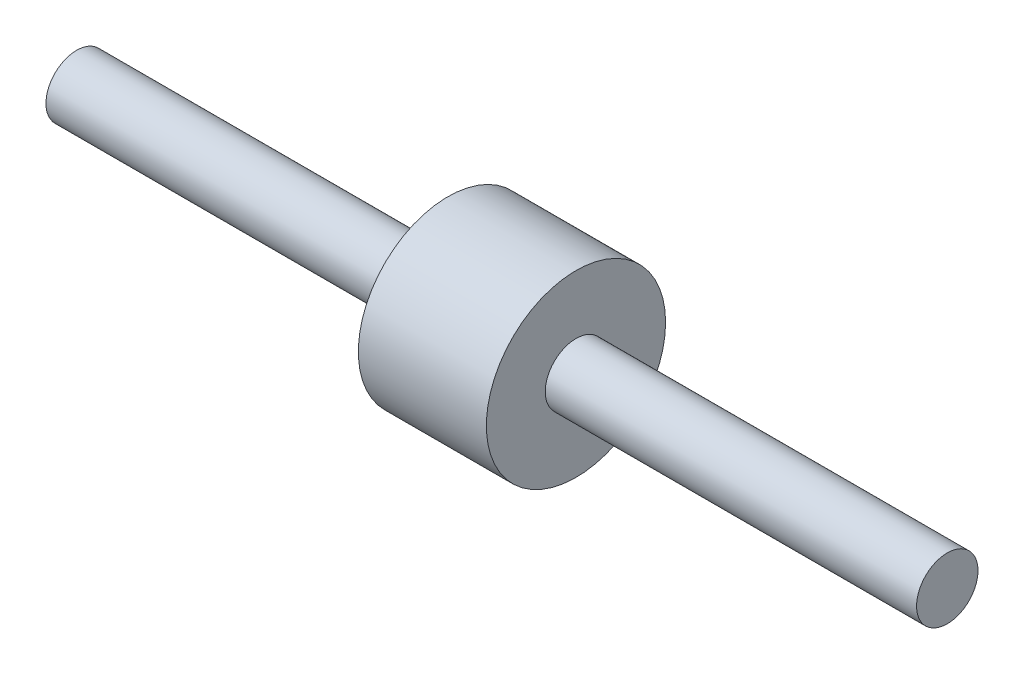
SolidWorks part; units mm, degrees
ref_plane "Alzado" through (0, 0, 0) normal (0, 0, 1) x (1, 0, 0)
ref_plane "Planta" through (0, 0, 0) normal (0, 1, 0) x (1, 0, 0)
ref_plane "Vista lateral" through (0, 0, 0) normal (1, 0, 0) x (0, 0, -1)
sketch "Croquis1" plane through (0, 0, 0) normal (1, 0, 0) x (0, 0, -1)
  circle A0 centre (0, 0) radius 17.5
  dimension "D1" = 35
extrude "Saliente-Extruir1" add sketch "Croquis1" along normal mid plane 25
sketch "Croquis2" plane through (12.5, 0, 0) normal (1, 0, 0) x (0, 0, -1)
  circle A0 centre (0, 0) radius 6
  dimension "D1" = 12
extrude "Saliente-Extruir2" add sketch "Croquis2" along normal blind 72.5
mirror "Simetría1" about plane through (0, 0, 0) normal (1, 0, 0) of "Saliente-Extruir2"
